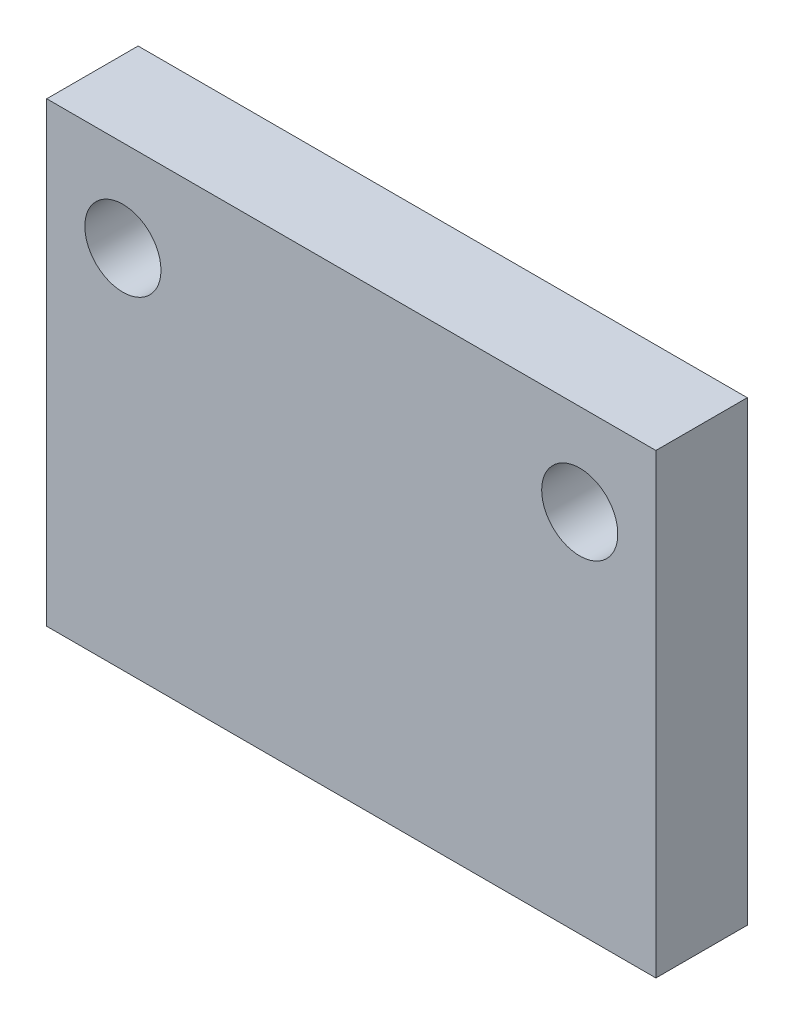
SolidWorks part; units mm, degrees
material "Thornel VCB-20 碳布"
ref_plane "前视基准面" through (0, 0, 0) normal (0, 0, 1) x (1, 0, 0)
ref_plane "上视基准面" through (0, 0, 0) normal (0, 1, 0) x (1, 0, 0)
ref_plane "右视基准面" through (0, 0, 0) normal (1, 0, 0) x (0, 0, -1)
sketch "草图1" plane through (0, 0, 0) normal (0, 0, 1) x (1, 0, 0)
  line L1 (-10, 7.5) -> (10, 7.5)
  line L2 (-10, 7.5) -> (-10, -7.5)
  line L3 (-10, -7.5) -> (10, -7.5)
  line L4 (10, 7.5) -> (10, -7.5)
  line L5 (0, -7.5) -> (0, 7.5) construction
  line L6 (-10, 0) -> (10, 0) construction
  circle A0 centre (-7.5, 4.5) radius 1.25
  circle A1 centre (7.5, 4.5) radius 1.25
  point P0 (0, 0)
  dimension "D3" = 2.5
  dimension "D4" = 15
  dimension "D5" = 3
  dimension "D1" = 20
  dimension "D2" = 15
extrude "凸台-拉伸1" add sketch "草图1" along normal blind 3
